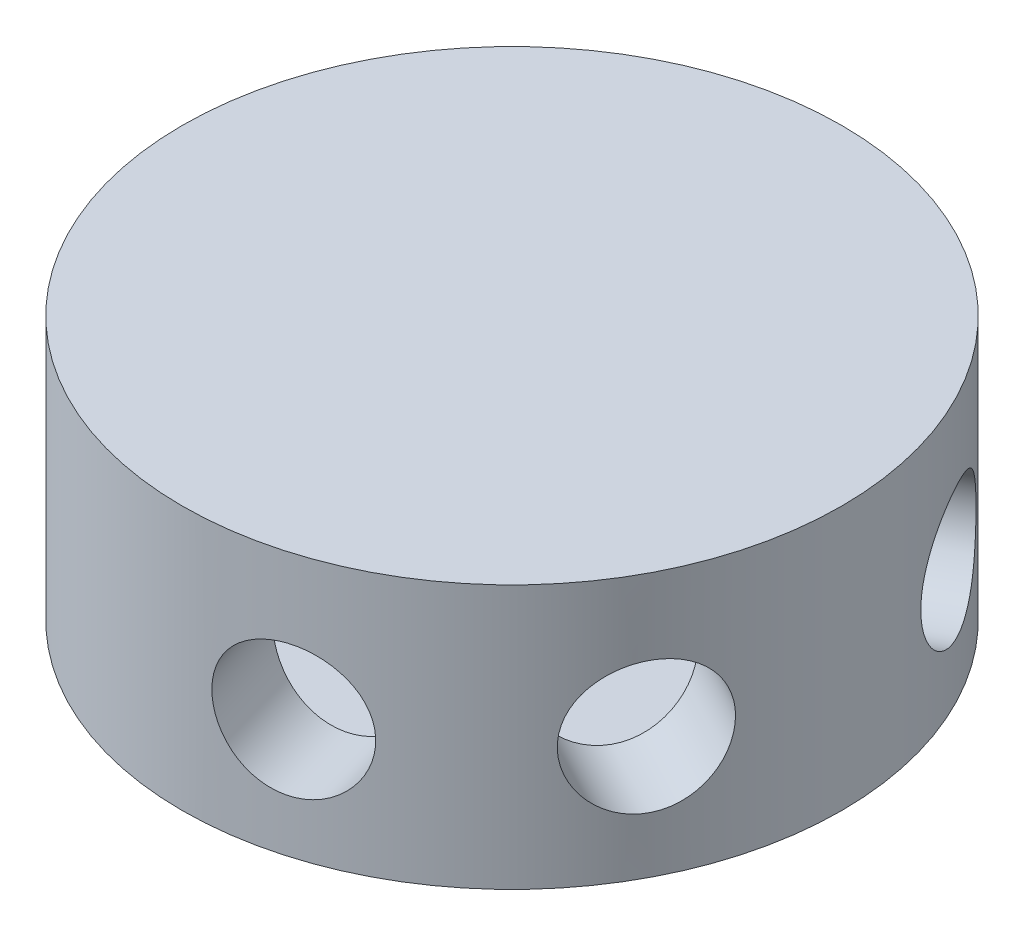
SolidWorks part; units mm, degrees
ref_plane "Front Plane" through (0, 0, 0) normal (0, 0, 1) x (1, 0, 0)
ref_plane "Top Plane" through (0, 0, 0) normal (0, 1, 0) x (1, 0, 0)
ref_plane "Right Plane" through (0, 0, 0) normal (1, 0, 0) x (0, 0, -1)
sketch "Sketch6" plane through (0, 0, 0) normal (0, 1, 0) x (1, 0, 0)
  circle A0 centre (0, 0) radius 15
  dimension "D1" = 30
extrude "Boss-Extrude3" add sketch "Sketch6" along normal blind 12
sketch "Sketch8" plane through (0, 12, 0) normal (0, 1, 0) x (1, 0, 0)
  circle A0 centre (0, 0) radius 11
  dimension "D1" = 22
extrude "Cut-Extrude3" cut sketch "Sketch8" against normal blind 8 from offset 2 offset against normal yes
hole_wizard "Ø6.0 (6) Diameter Hole3" positions "3DSketch3" profile "Sketch9" hole size "Ø6.0" standard "ANSI Metric"
sketch3d "3DSketch3"
  line L0 (0, 12, 0) -> (0, 0, 0) construction
  point P0 (13.2574, 5.5541, 7.0172)
  point P2 (13.2693, 5.5012, -6.9948)
  point P5 (0, 5.4483, 0)
  point P9 (0, 5.4483, 0)
  point P11 (0, 5.4483, 0)
  point P13 (0, 5.4483, 0)
  point P15 (-4.2532, 5.3955, -14.3844)
sketch "Sketch9" plane through (13.2574, 5.5541, 7.0172) normal (0, 1, 0) x (0.4678, 0, -0.8838)
  line L0 (0, 0) -> (0, 35.2746)
  line L1 (0, 35.2746) -> (3, 35.2746)
  line L2 (3, 35.2746) -> (3, 0)
  line L5 (3, 0) -> (0, 0)
  line L11 (0, -6.35) -> (0, 107.95) construction
  dimension "Thru Hole Dia." = 6
  dimension "Thru Hole Depth" = 35.2746
